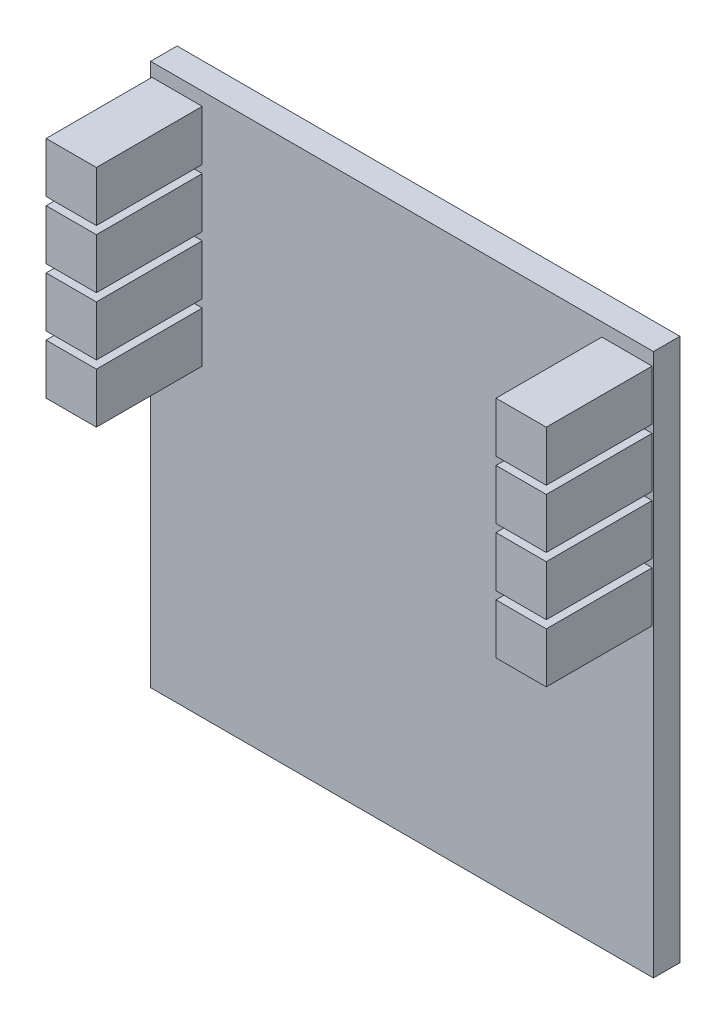
SolidWorks part; units mm, degrees
material "ﾎﾟﾘﾌﾟﾛﾋﾟﾚﾝ ﾎﾓﾎﾟﾘﾏｰ(PP Homopolymer)"
ref_plane "正面" through (0, 0, 0) normal (0, 0, 1) x (1, 0, 0)
ref_plane "平面" through (0, 0, 0) normal (0, 1, 0) x (1, 0, 0)
ref_plane "右側面" through (0, 0, 0) normal (1, 0, 0) x (0, 0, -1)
sketch "ｽｹｯﾁ1" plane through (0, 0, 0) normal (0, 0, 1) x (1, 0, 0)
  line L1 (0, 0) -> (19, 0)
  line L2 (0, 0) -> (0, 20.5)
  line L3 (0, 20.5) -> (19, 20.5)
  line L4 (19, 0) -> (19, 20.5)
  dimension "D1" = 19
  dimension "D2" = 20.5
extrude "ﾎﾞｽ - 押し出し1" add sketch "ｽｹｯﾁ1" along normal blind 1
sketch "ｽｹｯﾁ2" plane through (0, 0, 1) normal (0, 0, 1) x (1, 0, 0)
  line L0 (9.5, 0) -> (9.5, 20.5) construction
  line L1 (0.05, 20) -> (1.95, 20)
  line L2 (0.05, 20) -> (0.05, 18.1)
  line L3 (0.05, 18.1) -> (1.95, 18.1)
  line L4 (1.95, 20) -> (1.95, 18.1)
  line L5 (0, 20.5) -> (0, 0) construction
  line L6 (19, 20.5) -> (0, 20.5) construction
  line L7 (0, 0) -> (19, 0) construction
  line L8 (18.95, 20) -> (18.95, 18.1)
  line L9 (18.95, 18.1) -> (17.05, 18.1)
  line L10 (17.05, 20) -> (17.05, 18.1)
  line L11 (18.95, 20) -> (17.05, 20)
  line L12 (0.05, 17.8) -> (1.95, 17.8)
  line L13 (0.05, 17.8) -> (0.05, 15.9)
  line L14 (1.95, 17.8) -> (1.95, 15.9)
  line L15 (0.05, 15.9) -> (1.95, 15.9)
  line L16 (18.95, 17.8) -> (17.05, 17.8)
  line L17 (17.05, 17.8) -> (17.05, 15.9)
  line L18 (18.95, 17.8) -> (18.95, 15.9)
  line L19 (18.95, 15.9) -> (17.05, 15.9)
  line L20 (0.05, 15.6) -> (1.95, 15.6)
  line L21 (0.05, 15.6) -> (0.05, 13.7)
  line L22 (1.95, 15.6) -> (1.95, 13.7)
  line L23 (0.05, 13.7) -> (1.95, 13.7)
  line L24 (18.95, 15.6) -> (17.05, 15.6)
  line L25 (17.05, 15.6) -> (17.05, 13.7)
  line L26 (18.95, 15.6) -> (18.95, 13.7)
  line L27 (18.95, 13.7) -> (17.05, 13.7)
  line L28 (0.05, 13.4) -> (1.95, 13.4)
  line L29 (0.05, 13.4) -> (0.05, 11.5)
  line L30 (1.95, 13.4) -> (1.95, 11.5)
  line L31 (0.05, 11.5) -> (1.95, 11.5)
  line L32 (18.95, 13.4) -> (17.05, 13.4)
  line L33 (17.05, 13.4) -> (17.05, 11.5)
  line L34 (18.95, 13.4) -> (18.95, 11.5)
  line L35 (18.95, 11.5) -> (17.05, 11.5)
  dimension "D1" = 1.9
  dimension "D2" = 1.9
  dimension "D3" = 0.05
  dimension "D4" = 0.5
  dimension "D6" = 2.2
  dimension "D5" = 4
extrude "ﾎﾞｽ - 押し出し2" add sketch "ｽｹｯﾁ2" along normal blind 4 separate body
sketch "ｽｹｯﾁ3" plane through (0, 0, 0) normal (0, 0, -1) x (-1, 0, 0)
  line L0 (0, 0) -> (-19, 0) construction
  line L1 (-9, 0) -> (0, 0)
  line L2 (-9, 0) -> (-9, 8)
  line L3 (-9, 8) -> (0, 8)
  line L4 (0, 0) -> (0, 8)
  line L5 (0, 20.5) -> (0, 0) construction
  dimension "D1" = 9
  dimension "D2" = 8
extrude "ﾎﾞｽ - 押し出し3" add sketch "ｽｹｯﾁ3" along normal blind 2.5 separate body
sketch "ｽｹｯﾁ4" plane through (0, 0, -2.5) normal (0, 0, -1) x (-1, 0, 0)
  line L0 (0, 8) -> (-9, 8) construction
  line L1 (-1.5, 8) -> (0, 8)
  line L2 (-1.5, 8) -> (-1.5, 0)
  line L3 (-1.5, 0) -> (0, 0)
  line L4 (0, 8) -> (0, 0)
  dimension "D1" = 1.5
extrude "ﾎﾞｽ - 押し出し4" add sketch "ｽｹｯﾁ4" along normal blind 6
